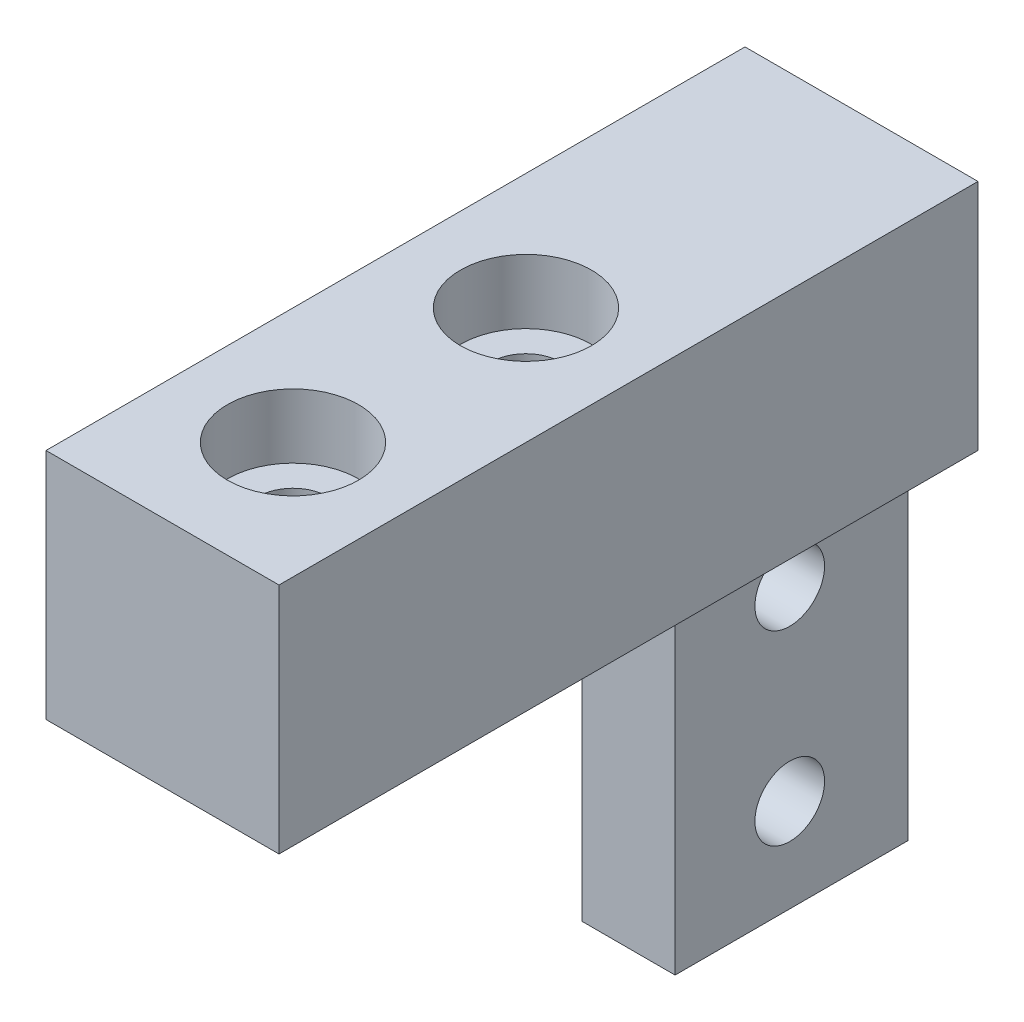
SolidWorks part; units mm, degrees
ref_plane "Front Plane" through (0, 0, 0) normal (0, 0, 1) x (1, 0, 0)
ref_plane "Top Plane" through (0, 0, 0) normal (0, 1, 0) x (1, 0, 0)
ref_plane "Right Plane" through (0, 0, 0) normal (1, 0, 0) x (0, 0, -1)
sketch "Sketch1" plane through (0, 0, 0) normal (1, 0, 0) x (0, 0, -1)
  line L1 (0, 0) -> (38.1, 0)
  line L2 (0, 0) -> (0, -12.7)
  line L3 (0, -12.7) -> (38.1, -12.7)
  line L4 (38.1, 0) -> (38.1, -12.7)
  dimension "D1" = 38.1
  dimension "D2" = 12.7
extrude "Boss-Extrude1" add sketch "Sketch1" along normal blind 12.7
sketch "Sketch2" plane through (0, -12.7, 0) normal (0, -1, 0) x (1, 0, 0)
  line L0 (0, 0) -> (0, -38.1) construction
  line L1 (12.7, -38.1) -> (0, -38.1)
  line L2 (12.7, -38.1) -> (12.7, -25.4)
  line L3 (12.7, -25.4) -> (0, -25.4)
  line L4 (0, -38.1) -> (0, -25.4)
  dimension "D1" = 12.7
extrude "Boss-Extrude2" add sketch "Sketch2" along normal blind 20.32
sketch "Sketch3" plane through (0, 0, -38.1) normal (0, 0, -1) x (-1, 0, 0)
  line L0 (-12.7, -12.7) -> (-8.89, -12.7)
  line L1 (-8.89, -12.7) -> (-8.89, -33.02)
  line L2 (0, -33.02) -> (-12.7, -33.02) construction
  line L3 (-3.81, -12.7) -> (-3.81, -33.02)
  line L4 (-12.7, -33.02) -> (-12.7, 0) construction
  line L5 (0, -33.02) -> (0, 0) construction
  line L6 (-3.81, -12.7) -> (0, -12.7)
  line L8 (-12.7, -12.7) -> (-12.7, -33.02)
  line L9 (-12.7, -33.02) -> (-8.89, -33.02)
  line L13 (-3.81, -33.02) -> (0, -33.02)
  line L14 (0, -12.7) -> (0, -33.02)
  dimension "D1" = 3.81
  dimension "D2" = 3.81
extrude "Cut-Extrude1" cut sketch "Sketch3" against normal blind 12.7
sketch "Sketch4" plane through (8.89, 0, 0) normal (1, 0, 0) x (0, 0, -1)
  line L0 (38.1, -33.02) -> (38.1, -12.7) construction
  line L1 (0, -12.7) -> (38.1, -12.7) construction
  point P0 (31.648, -17.78)
  point P1 (31.648, -27.94)
  dimension "D1" = 6.452
  dimension "D2" = 6.452
  dimension "D3" = 5.08
  dimension "D4" = 10.16
hole_wizard "#6 Clearance Hole1" positions "Sketch5" profile "Sketch6" hole size "#6" standard "ANSI Inch"
sketch "Sketch5" plane through (8.89, 0, 0) normal (1, 0, 0) x (0, 0, -1)
  point P0 (31.648, -17.78)
  point P3 (31.648, -27.94)
  point P6 (44.5096, -23.7061)
  point P7 (0, 0)
sketch "Sketch6" plane through (8.89, -17.78, -31.648) normal (0, 1, 0) x (0, 0, -1)
  line L0 (0, 0) -> (0, 11.3008)
  line L1 (0, 11.3008) -> (1.8986, 10.16)
  line L2 (1.8986, 10.16) -> (1.8986, 0)
  line L5 (1.8986, 0) -> (0, 0)
  line L10 (0, 11.3008) -> (-1.8987, 10.16) construction
  line L11 (0, -6.35) -> (0, 107.95) construction
  dimension "Hole Dia." = 3.7973
  dimension "Hole Depth" = 10.16
  dimension "Drill Angle" = 118
sketch "Sketch7" plane through (0, 0, 0) normal (0, 1, 0) x (1, 0, 0)
  line L0 (0, 38.1) -> (0, 0) construction
  line L1 (12.7, 0) -> (0, 0) construction
  point P0 (6.35, 7.112)
  point P1 (6.35, 19.812)
  dimension "D1" = 6.35
  dimension "D2" = 6.35
  dimension "D3" = 7.112
  dimension "D4" = 12.7
hole_wizard "CBORE for #6 Socket Head Cap Screw1" positions "Sketch8" profile "Sketch9" counterbore size "#6" standard "ANSI Inch" end condition through all
sketch "Sketch8" plane through (0, 0, 0) normal (0, 1, 0) x (1, 0, 0)
  point P0 (6.35, 7.112)
  point P3 (6.35, 19.812)
sketch "Sketch9" plane through (6.35, 0, -7.112) normal (1, 0, 0) x (0, 0, 1)
  line L0 (0, 0) -> (0, 33.02)
  line L1 (0, 33.02) -> (1.8986, 33.02)
  line L3 (1.8986, 33.02) -> (1.8986, 3.5052)
  line L4 (1.8986, 3.5052) -> (3.5725, 3.5052)
  line L5 (3.5725, 3.5052) -> (3.5725, 0)
  line L7 (3.5725, 0) -> (0, 0)
  line L11 (0, -6.35) -> (0, 107.95) construction
  dimension "Thru Hole Dia." = 3.7973
  dimension "Thru Hole Depth" = 33.02
  dimension "C'Bore Dia." = 7.145
  dimension "C'Bore Depth" = 3.5052
